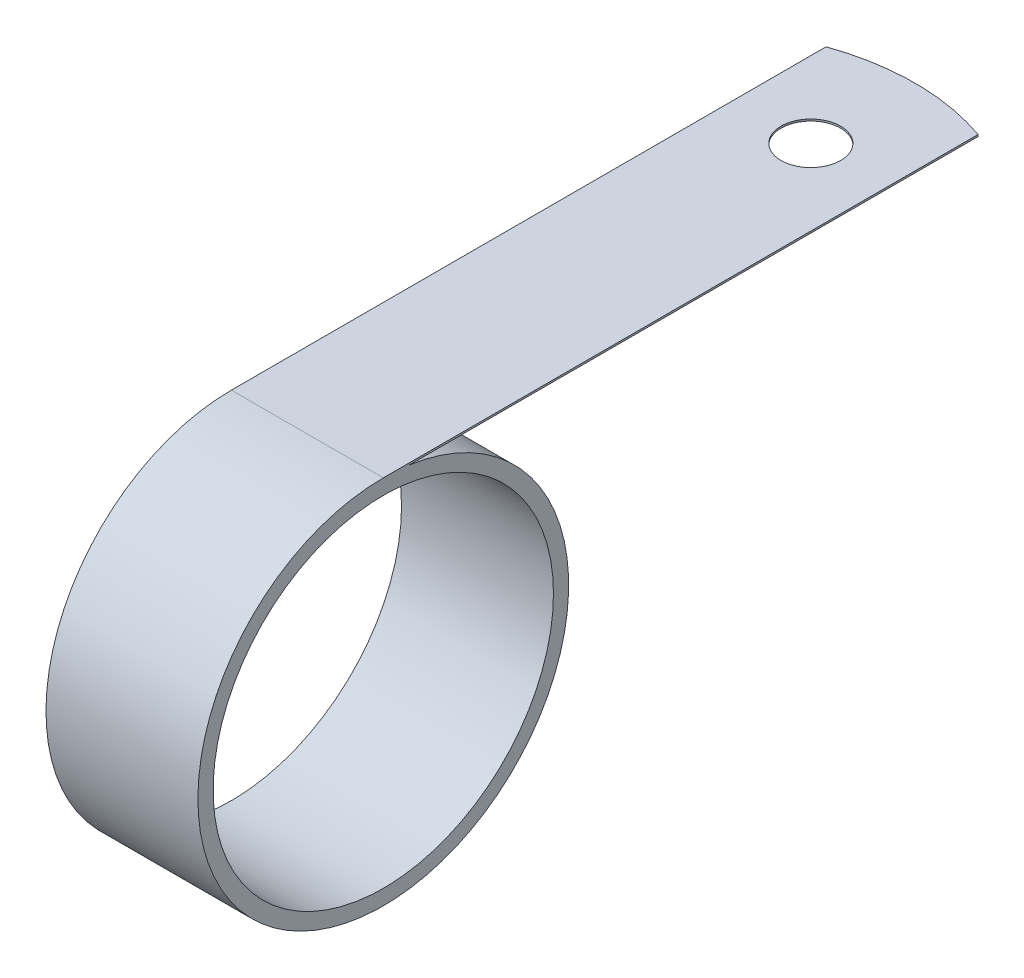
SolidWorks part; units mm, degrees
ref_plane "Front" through (0, 0, 0) normal (0, 0, 1) x (1, 0, 0)
ref_plane "Top" through (0, 0, 0) normal (0, 1, 0) x (1, 0, 0)
ref_plane "Right" through (0, 0, 0) normal (1, 0, 0) x (0, 0, -1)
sketch "Sketch1" plane through (0, 0, 0) normal (1, 0, 0) x (0, 0, -1)
  line L0 (0, 15.494) -> (50.8, 15.494)
  line L1 (2.1678, 15.3416) -> (50.8, 15.3416)
  line L2 (50.8, 15.3416) -> (50.8, 15.494)
  line L3 (0, 15.494) -> (0, -15.494) construction
  circle A0 centre (0, 0) radius 14.224
  arc A1 (0, 15.494) -> (2.1678, 15.3416) centre (0, 0) ccw
  dimension "D2" = 50.8
extrude "Boss-Extrude1" add sketch "Sketch1" along normal mid plane 12.7
sketch "Sketch2" plane through (0, 15.494, 0) normal (0, 1, 0) x (1, 0, 0)
  line L0 (0, 31.75) -> (0, 50.8) construction
  line L1 (6.35, 50.8) -> (-6.35, 50.8) construction
  line L2 (-6.35, 49.7105) -> (-6.35, 51.435)
  line L3 (-6.35, 50.8) -> (-6.35, 0) construction
  line L4 (-6.35, 51.435) -> (6.35, 51.435)
  line L5 (6.35, 49.7105) -> (6.35, 51.435)
  line L6 (6.35, 50.8) -> (6.35, 0) construction
  arc A0 (6.35, 49.7105) -> (-6.35, 49.7105) centre (0, 31.75) ccw
  circle A1 centre (0, 42.0878) radius 2.4892
  dimension "D2" = 0.635
extrude "OneHole" cut sketch "Sketch2" against normal up to next
sketch "Sketch4" plane through (0, 15.494, 0) normal (0, 1, 0) x (1, 0, 0)
  line L0 (0, 50.8) -> (0, 42.0878) construction
  line L2 (9.525, 42.0878) -> (-9.525, 42.0878) construction
  circle A0 centre (-9.525, 42.0878) radius 2.4892
  circle A1 centre (9.525, 42.0878) radius 2.4892
  dimension "D1" = 4.9784
  dimension "D2" = 8.7122
  dimension "D3" = 19.05
extrude "TwoHole" [suppressed] cut sketch "Sketch4" against normal up to next
equation "\"D2@Sketch1\"=2"
equation "\"D1@Sketch4\" = \"HoleDia@Sketch2\""
equation "\"D2@Sketch4\" = \"HolePosition@Sketch2\""
